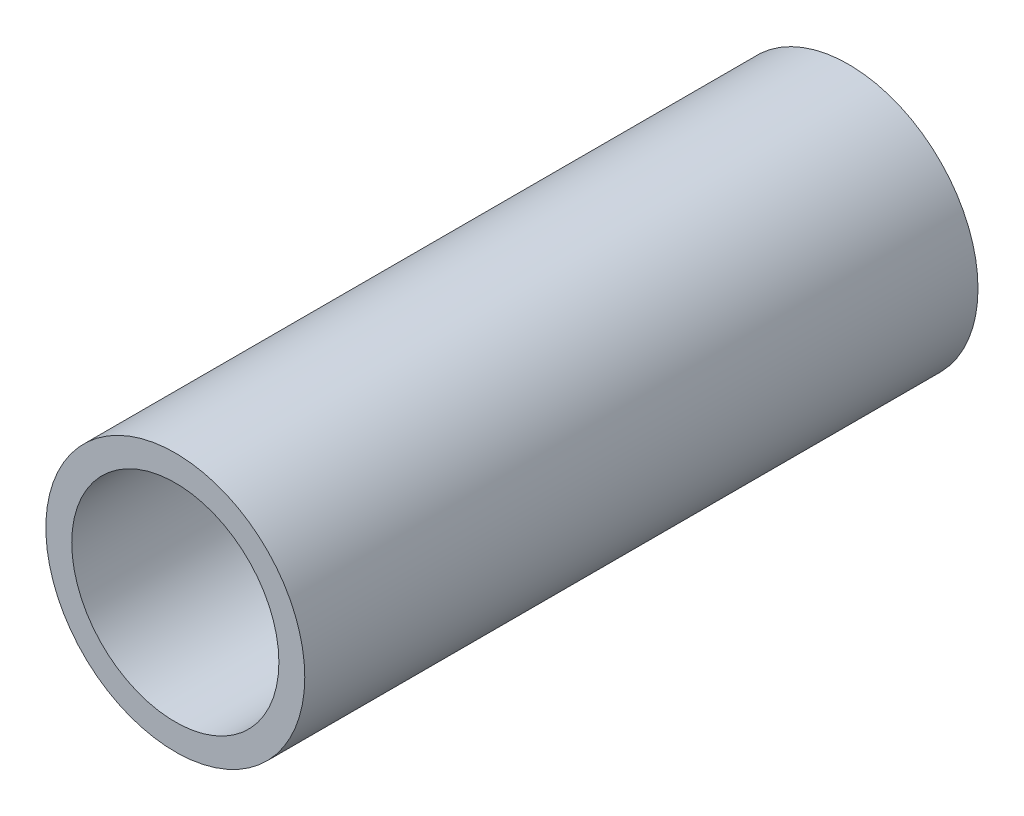
SolidWorks part; units mm, degrees
ref_plane "Front Plane" through (0, 0, 0) normal (0, 0, 1) x (1, 0, 0)
ref_plane "Top Plane" through (0, 0, 0) normal (0, 1, 0) x (1, 0, 0)
ref_plane "Right Plane" through (0, 0, 0) normal (1, 0, 0) x (0, 0, -1)
sketch "Sketch1" plane through (0, 0, 0) normal (0, 0, 1) x (1, 0, 0)
  circle A0 centre (0, 0) radius 1.25
  circle A1 centre (0, 0) radius 1
extrude "Boss-Extrude1" add sketch "Sketch1" along normal blind 6.5
